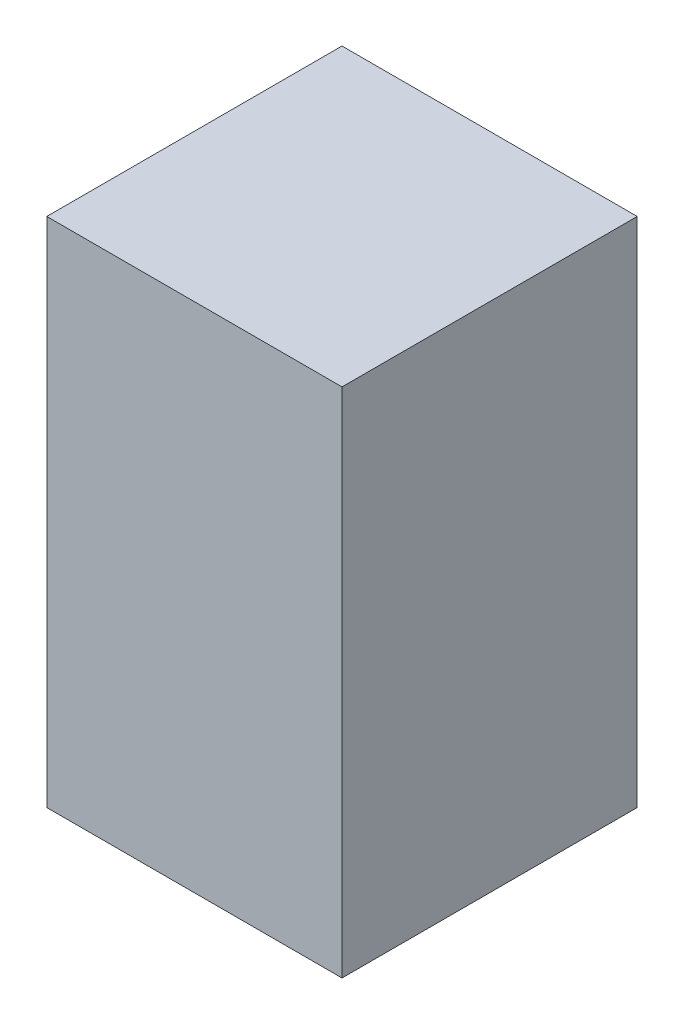
SolidWorks part; units mm, degrees
ref_plane "Front Plane" through (0, 0, 0) normal (0, 0, 1) x (1, 0, 0)
ref_plane "Top Plane" through (0, 0, 0) normal (0, 1, 0) x (1, 0, 0)
ref_plane "Right Plane" through (0, 0, 0) normal (1, 0, 0) x (0, 0, -1)
sketch "Sketch1" plane through (0, 0, 0) normal (0, 1, 0) x (1, 0, 0)
  line L1 (-250, -250) -> (250, -250)
  line L2 (-250, -250) -> (-250, 250)
  line L3 (-250, 250) -> (250, 250)
  line L4 (250, -250) -> (250, 250)
  line L5 (-250, -250) -> (250, 250) construction
  line L6 (-250, 250) -> (250, -250) construction
  point P0 (0, 0)
  dimension "D1" = 500
  dimension "D2" = 500
extrude "Boss-Extrude1" add sketch "Sketch1" along normal blind 807 and the other way blind 60
